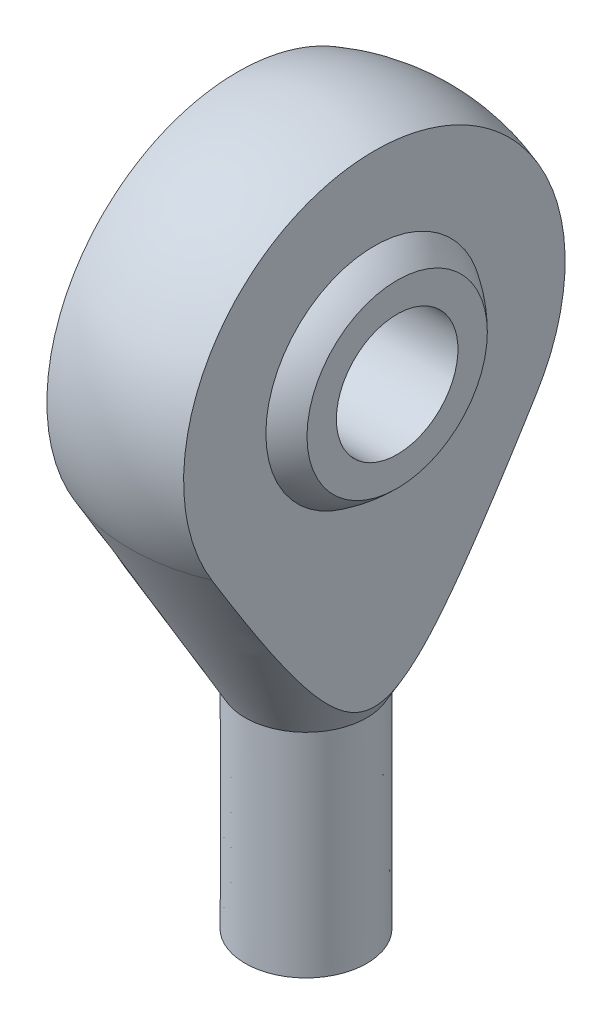
SolidWorks part; units mm, degrees
ref_plane "Płaszczyzna XY" through (0, 0, 0) normal (0, 0, 1) x (1, 0, 0)
ref_plane "Płaszczyzna XZ" through (0, 0, 0) normal (0, 1, 0) x (1, 0, 0)
ref_plane "Płaszczyzna YZ" through (0, 0, 0) normal (1, 0, 0) x (0, 0, -1)
sketch "Szkic1" plane through (0, 0, 0) normal (0, 0, 1) x (1, 0, 0)
  line L0 (-3, 0) -> (3, 0)
  line L1 (3, 0) -> (3, 21)
  line L2 (3, 21) -> (-3, 21) construction
  line L3 (-3, 21) -> (-3, 0)
  line L4 (-3, 21) -> (-8.6992, 31.0772)
  line L5 (3, 21) -> (8.7057, 31.0704)
  line L6 (0.0052, 46) -> (0, 0)
  arc A0 (8.7057, 31.0704) -> (-8.6992, 31.0772) centre (0.0052, 36) ccw
  point P4 (0, 0)
  dimension "D2" = 20
  dimension "D1" = 6
  dimension "D3" = 36
  dimension "GL" = 21
revolve "Obrót4" add sketch "Szkic1" angle 360 about L6
sketch "Szkic2" plane through (0, 0, 0) normal (0, 0, 1) x (1, 0, 0)
  line L0 (-20, 46) -> (20, 46)
  line L1 (20, 46) -> (20, 10.8573)
  line L2 (20, 10.8573) -> (3.375, 21.6537)
  line L3 (3.375, 21.6537) -> (3.375, 46)
  line L4 (-20, 46) -> (-20, 10.8667)
  line L5 (-20, 10.8667) -> (-3.375, 21.6631)
  line L6 (-3.375, 21.6631) -> (-3.375, 46)
  line L7 (0, 35.7786) -> (0, -51.7786) construction
  line L8 (-8.6992, 31.0772) -> (-3, 21) construction
  line L9 (3.0047, 20.9993) -> (8.7062, 31.0753) construction
  point P9 (0, 46)
  point P12 (0, -8)
  dimension "M" = 6.75
  dimension "D1" = 3.375
  dimension "D2" = 40
  dimension "D3" = 54
  dimension "D4" = 123
  dimension "D5" = 123
extrude "Wytnij-wyciągnięcie1" cut sketch "Szkic2" against normal through all both and the other way through all contours L5 L6 L0 L4 | L3 L2 L1 L0
sketch "Szkic3" plane through (0, 0, 0) normal (1, 0, 0) x (0, 0, -1)
  line L3 (0, 0) -> (0, 10.5388) construction
ref_plane "Płaszczyzna1" through (0, 0, 0) normal (0, 0, -1) x (0, 1, 0)
sketch "Szkic4" plane through (0, 0, 0) normal (0, 0, -1) x (0, 1, 0)
  line L0 (-200000, 0) -> (200010.5388, 0) construction
  line L1 (35.9993, -1) -> (35.9993, 16.5523) construction
  line L2 (31.5493, -4.5) -> (40.4493, -4.5)
  line L3 (31.5493, -4.5) -> (31.5493, 4.5)
  line L4 (31.5493, 4.5) -> (40.4493, 4.5)
  line L5 (40.4493, -4.5) -> (40.4493, 4.5)
  line L6 (31.5493, -4.5) -> (40.4493, 4.5) construction
  line L7 (31.5493, 4.5) -> (40.4493, -4.5) construction
  line L8 (32.9993, -4.5) -> (38.9993, -4.5)
  line L9 (32.9993, -4.5) -> (32.9993, 4.5)
  line L10 (32.9993, 4.5) -> (38.9993, 4.5)
  line L11 (38.9993, -4.5) -> (38.9993, 4.5)
  line L12 (32.9993, -4.5) -> (38.9993, 4.5) construction
  line L13 (32.9993, 4.5) -> (38.9993, -4.5) construction
  circle A0 centre (35.9993, 0) radius 6.3287
  dimension "D1" = 6
  dimension "D2" = 8.9
  dimension "D3" = 9
  dimension "D4" = 36
revolve "Obrót5" add sketch "Szkic4" angle 360 about L1
sketch "Szkic8" plane through (0, 0, 0) normal (1, 0, 0) x (0, 0, -1)
  circle A0 centre (0, 35.9993) radius 3
extrude "Wytnij-wyciągnięcie3" cut sketch "Szkic8" against normal through all both and the other way through all
sketch "Szkic9" [suppressed] plane through (0, 0, 0) normal (1, 0, 0) x (0, 0, -1)
  circle A0 centre (0, 41.9991) radius 4
extrude "Wytnij-wyciągnięcie4" [suppressed] cut sketch "Szkic9" against normal through all both and the other way through all
ref_point "Point1"
sketch "Sketch2" plane through (0, 0, 0) normal (1, 0, 0) x (0, 0, -1)
  line L10 (-8.625, -1.8186) -> (10.3296, -1.8186)
  line L11 (-8.625, -1.8186) -> (-8.625, 10.4997)
  line L12 (-8.625, 10.4997) -> (10.3296, 10.4997)
  line L13 (10.3296, -1.8186) -> (10.3296, 10.4997)
  line L14 (-2.9998, -1.8186) -> (-0.7841, -1.8186)
extrude "Cut-Extrude2" cut sketch "Sketch2" against normal through all both and the other way through all contours L10 L13 L12 L11
equation "\"D2@Szkic2\"=2*\"D2@Szkic1\""
equation "\"D1@Szkic2\"=\"M@Szkic2\"/2mm"
